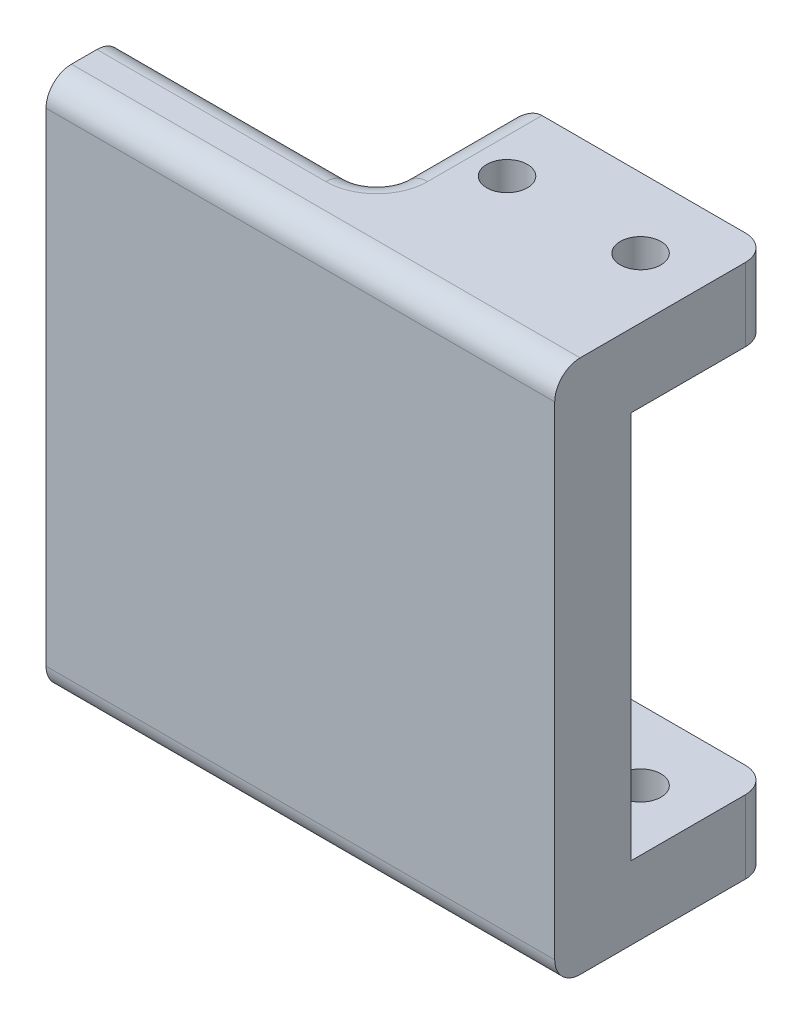
SolidWorks part; units mm, degrees
ref_plane "Front Plane" through (0, 0, 0) normal (0, 0, 1) x (1, 0, 0)
ref_plane "Top Plane" through (0, 0, 0) normal (0, 1, 0) x (1, 0, 0)
ref_plane "Right Plane" through (0, 0, 0) normal (1, 0, 0) x (0, 0, -1)
sketch "Sketch1" plane through (0, 0, 0) normal (0, 1, 0) x (1, 0, 0)
  line L0 (5.25, 0) -> (-5.25, 0) construction
  line L1 (-10, 5.5) -> (10, 5.5)
  line L2 (-10, 5.5) -> (-10, -5.5)
  line L3 (-10, -5.5) -> (10, -5.5)
  line L4 (10, 5.5) -> (10, -5.5)
  line L5 (0, -5.5) -> (0, 5.5) construction
  line L6 (-10, 0) -> (10, 0) construction
  line L8 (10, -5.5) -> (-30, -5.5)
  line L9 (10, -5.5) -> (10, -11.5)
  line L10 (10, -11.5) -> (-30, -11.5)
  line L11 (-30, -5.5) -> (-30, -11.5)
  line L12 (-10, -11.5) -> (-10, -5.5) construction
  line L13 (10, -8.5) -> (-30, -8.5) construction
  circle A0 centre (-5.25, 0) radius 1.6
  circle A1 centre (5.25, 0) radius 1.6
  point P0 (0, 0)
  point P7 (0, 0)
  point P358 (-10, -8.5)
  dimension "D4" = 3.2
  dimension "D1" = 11
  dimension "D2" = 20
  dimension "D3" = 10.5
  dimension "D5" = 40
  dimension "D6" = 6
extrude "Boss-Extrude1" add sketch "Sketch1" along normal blind 42 contours L4 L1 L2 L3 A1 A0 | L8 L11 L10 L9 L3
sketch "Sketch2" plane through (0, 0, -5.5) normal (0, 0, -1) x (-1, 0, 0)
  line L0 (10, 21) -> (-10, 21) construction
  line L1 (10, 42) -> (10, 0) construction
  line L2 (-10, 42) -> (-10, 0) construction
  line L4 (10, 36.25) -> (-10, 36.25)
  line L5 (10, 36.25) -> (10, 5.75)
  line L6 (10, 5.75) -> (-10, 5.75)
  line L7 (-10, 36.25) -> (-10, 5.75)
  line L8 (0, 5.75) -> (0, 36.25) construction
  line L9 (10, 21) -> (-10, 21) construction
  point P6 (0, 21)
  dimension "D1" = 30.5
extrude "Cut-Extrude1" cut sketch "Sketch2" against normal blind 11
fillet "Fillet1" radius 2 12 edges at (-10, 0, 0) (-10, 42, 0) (-10, 0, 11.5) (-10, 42, 11.5) (-20, 0, 5.5) (-20, 42, 5.5) (-10, 39.125, 5.5) (-10, 2.875, 5.5) (10, 2.875, -5.5) (-10, 2.875, -5.5) (-10, 39.125, -5.5) (10, 39.125, -5.5)
